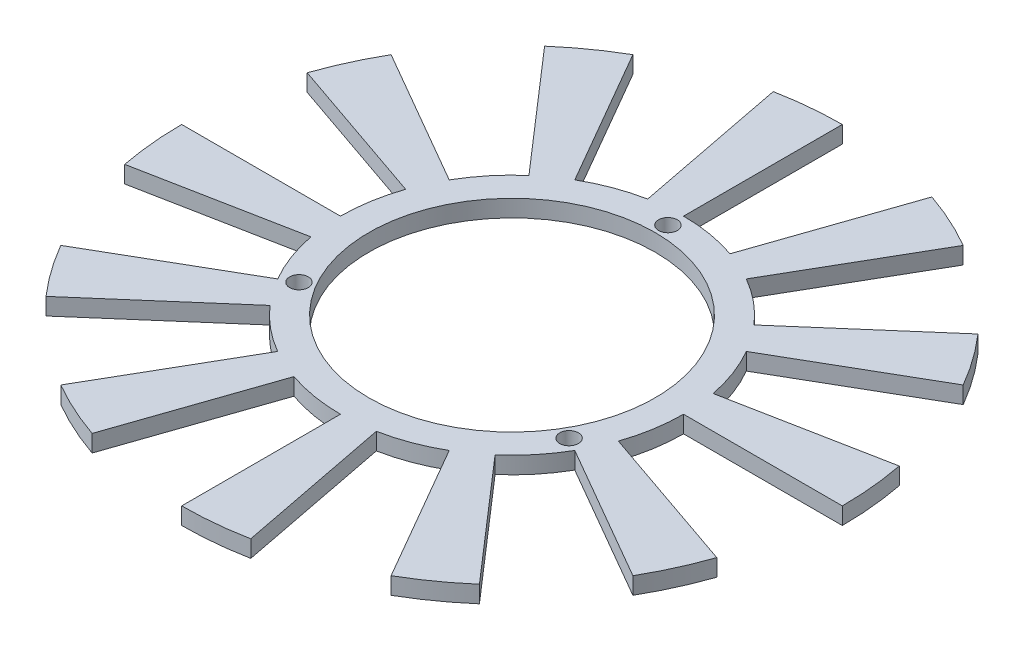
SolidWorks part; units mm, degrees
material "AISI 1010 Steel, hot rolled bar"
ref_plane "Front Plane" through (0, 0, 0) normal (0, 0, 1) x (1, 0, 0)
ref_plane "Top Plane" through (0, 0, 0) normal (0, 1, 0) x (1, 0, 0)
ref_plane "Right Plane" through (0, 0, 0) normal (1, 0, 0) x (0, 0, -1)
sketch "Sketch1" plane through (0, 0, 0) normal (0, 1, 0) x (1, 0, 0)
  circle A0 centre (0, 0) radius 25.25
  dimension "D1" = 50.5
extrude "Extrude-Thin1" add sketch "Sketch1" against normal blind 3 thin
sketch "Sketch2" plane through (0, 0, 0) normal (0, 1, 0) x (1, 0, 0)
  line L0 (0, -30.25) -> (0, 30.25) construction
  line L1 (0, 0) -> (23.8157, -13.75) construction
  line L2 (0, 0) -> (-23.8157, -13.75) construction
  circle A0 centre (0, 27.5) radius 1.65
  circle A1 centre (0, 0) radius 30.25 construction
  circle A4 centre (0, 0) radius 27.5 construction
  circle A7 centre (23.8157, -13.75) radius 1.65
  circle A8 centre (-23.8157, -13.75) radius 1.65
  dimension "D1" = 55
  dimension "D2" = 3.3
  dimension "D3" = 120
  dimension "D4" = 120
extrude "Cut-Extrude3" cut sketch "Sketch2" against normal blind 10
sketch "Sketch5" plane through (0, -3, 0) normal (0, -1, 0) x (1, 0, 0)
  line L0 (0, 0) -> (0, 35.9971) construction
  line L1 (0, 0) -> (6.5079, 33.4801) construction
  line L2 (0, 58.25) -> (0, 30.25)
  line L3 (5.772, 29.6942) -> (11.1146, 57.1798)
  line L4 (29.125, 50.446) -> (15.125, 26.1973)
  line L5 (19.8458, 22.83) -> (38.2154, 43.9618)
  line L6 (50.446, 29.125) -> (26.1973, 15.125)
  line L7 (28.6019, 9.8484) -> (55.0765, 18.9643)
  line L8 (58.25, 0) -> (30.25, 0)
  line L9 (29.6942, -5.772) -> (57.1798, -11.1146)
  line L10 (50.446, -29.125) -> (26.1973, -15.125)
  line L11 (22.83, -19.8458) -> (43.9618, -38.2154)
  line L12 (29.125, -50.446) -> (15.125, -26.1973)
  line L13 (9.8484, -28.6019) -> (18.9643, -55.0765)
  line L14 (0, -58.25) -> (0, -30.25)
  line L15 (-5.772, -29.6942) -> (-11.1146, -57.1798)
  line L16 (-29.125, -50.446) -> (-15.125, -26.1973)
  line L17 (-19.8458, -22.83) -> (-38.2154, -43.9618)
  line L18 (-50.446, -29.125) -> (-26.1973, -15.125)
  line L19 (-28.6019, -9.8484) -> (-55.0765, -18.9643)
  line L20 (-58.25, 0) -> (-30.25, 0)
  line L21 (-29.6942, 5.772) -> (-57.1798, 11.1146)
  line L22 (-50.446, 29.125) -> (-26.1973, 15.125)
  line L23 (-22.83, 19.8458) -> (-43.9618, 38.2154)
  line L24 (-29.125, 50.446) -> (-15.125, 26.1973)
  line L25 (-9.8484, 28.6019) -> (-18.9643, 55.0765)
  circle A0 centre (0, 0) radius 30.25 construction
  arc A1 (5.772, 29.6942) -> (0, 30.25) centre (0, 0) ccw
  arc A2 (11.1146, 57.1798) -> (0, 58.25) centre (0, 0) ccw
  arc A3 (38.2154, 43.9618) -> (29.125, 50.446) centre (0, 0) ccw
  arc A4 (19.8458, 22.83) -> (15.125, 26.1973) centre (0, 0) ccw
  arc A5 (55.0765, 18.9643) -> (50.446, 29.125) centre (0, 0) ccw
  arc A6 (28.6019, 9.8484) -> (26.1973, 15.125) centre (0, 0) ccw
  arc A7 (57.1798, -11.1146) -> (58.25, 0) centre (0, 0) ccw
  arc A8 (29.6942, -5.772) -> (30.25, 0) centre (0, 0) ccw
  arc A9 (43.9618, -38.2154) -> (50.446, -29.125) centre (0, 0) ccw
  arc A10 (22.83, -19.8458) -> (26.1973, -15.125) centre (0, 0) ccw
  arc A11 (18.9643, -55.0765) -> (29.125, -50.446) centre (0, 0) ccw
  arc A12 (9.8484, -28.6019) -> (15.125, -26.1973) centre (0, 0) ccw
  arc A13 (-11.1146, -57.1798) -> (0, -58.25) centre (0, 0) ccw
  arc A14 (-5.772, -29.6942) -> (0, -30.25) centre (0, 0) ccw
  arc A15 (-38.2154, -43.9618) -> (-29.125, -50.446) centre (0, 0) ccw
  arc A16 (-19.8458, -22.83) -> (-15.125, -26.1973) centre (0, 0) ccw
  arc A17 (-55.0765, -18.9643) -> (-50.446, -29.125) centre (0, 0) ccw
  arc A18 (-28.6019, -9.8484) -> (-26.1973, -15.125) centre (0, 0) ccw
  arc A19 (-57.1798, 11.1146) -> (-58.25, 0) centre (0, 0) ccw
  arc A20 (-29.6942, 5.772) -> (-30.25, 0) centre (0, 0) ccw
  arc A21 (-43.9618, 38.2154) -> (-50.446, 29.125) centre (0, 0) ccw
  arc A22 (-22.83, 19.8458) -> (-26.1973, 15.125) centre (0, 0) ccw
  arc A23 (-18.9643, 55.0765) -> (-29.125, 50.446) centre (0, 0) ccw
  arc A24 (-9.8484, 28.6019) -> (-15.125, 26.1973) centre (0, 0) ccw
  point P87 (0, 0)
  dimension "D2" = 28
  dimension "D1" = 11
  dimension "D3" = 12
extrude "Boss-Extrude1" add sketch "Sketch5" against normal blind 3
